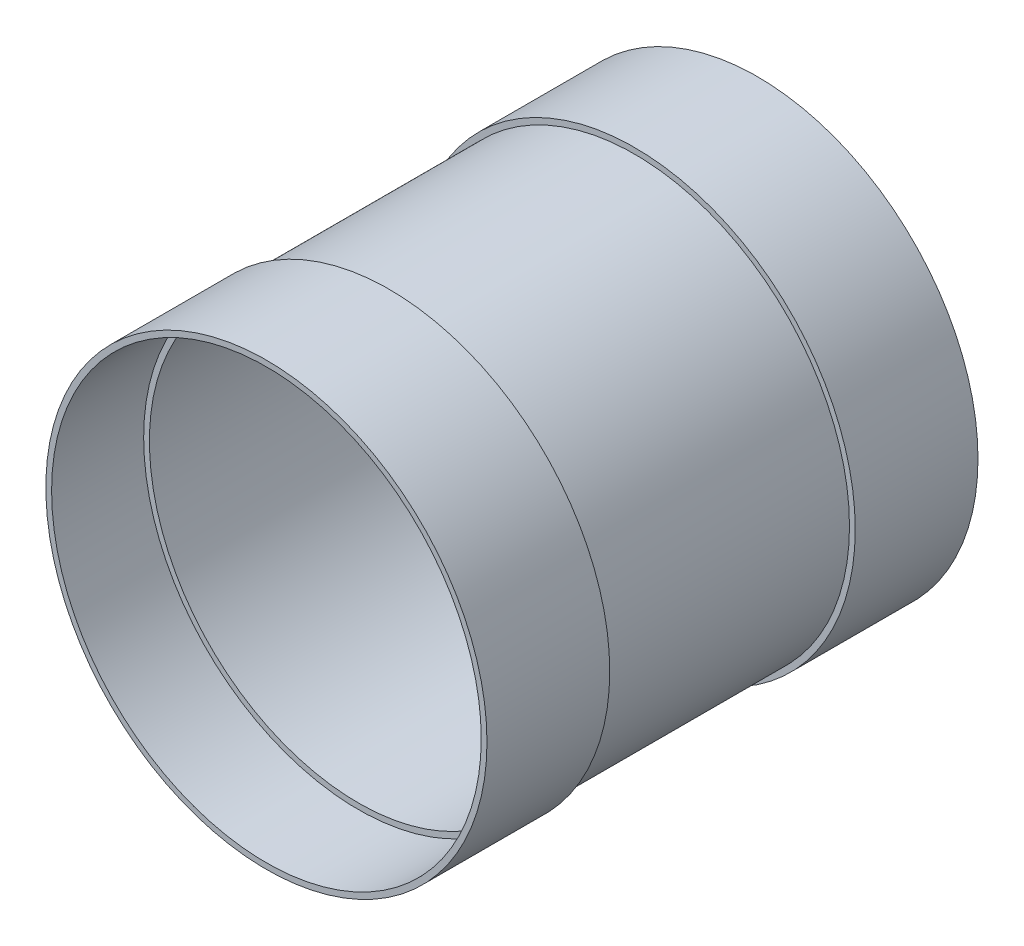
SolidWorks part; units mm, degrees
ref_plane "Front" through (0, 0, 0) normal (0, 0, 1) x (1, 0, 0)
ref_plane "Top" through (0, 0, 0) normal (0, 1, 0) x (1, 0, 0)
ref_plane "Right" through (0, 0, 0) normal (1, 0, 0) x (0, 0, -1)
sketch "Sketch2" plane through (0, 0, 0) normal (1, 0, 0) x (0, 0, -1)
  line L0 (-62.5946, 0) -> (53.5645, 0) construction
  line L1 (-203.2, 182.5625) -> (-101.6, 182.5625)
  line L2 (-101.6, 182.5625) -> (-101.6, 177.8)
  line L7 (-101.6, 177.8) -> (-203.2, 177.8)
  line L8 (-203.2, 177.8) -> (-203.2, 182.5625)
  line L9 (0, 0) -> (0, 72.5353) construction
  line L11 (101.6, 182.5625) -> (203.2, 182.5625)
  line L12 (101.6, 182.5625) -> (101.6, 177.8)
  line L13 (101.6, 177.8) -> (203.2, 177.8)
  line L14 (203.2, 182.5625) -> (203.2, 177.8)
  point P13 (203.2, 180.1813)
  dimension "D1" = 101.6
  dimension "D2" = 4.7625
  dimension "D3" = 406.4
  dimension "D4" = 355.6
revolve "Revolve1" add sketch "Sketch2" angle 360 about L0
sketch "Sketch3" plane through (0, 0, 0) normal (1, 0, 0) x (0, 0, -1)
  line L1 (-127, 173.0375) -> (127, 173.0375)
  line L2 (-127, 173.0375) -> (-127, 177.8)
  line L3 (-127, 177.8) -> (127, 177.8)
  line L4 (127, 173.0375) -> (127, 177.8)
  line L6 (0, 0) -> (103.0496, 0) construction
  line L7 (-101.6, 177.8) -> (-203.2, 177.8) construction
  line L8 (-203.2, 182.5625) -> (-203.2, -182.5625) construction
  line L9 (203.2, -182.5625) -> (203.2, 182.5625) construction
  point P4 (0, 0)
  point P5 (-142.185, 177.8)
  point P6 (0, 0)
  dimension "D1" = 4.7625
  dimension "D2" = 76.2
  dimension "D3" = 76.2
revolve "Revolve2" add sketch "Sketch3" angle 360 about L6
